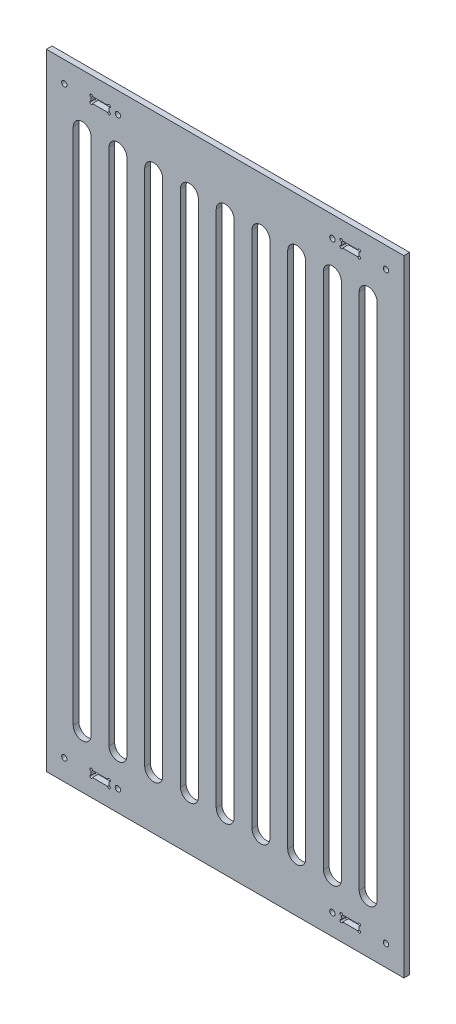
SolidWorks part; units mm, degrees
ref_plane "Front Plane" through (0, 0, 0) normal (0, 0, 1) x (1, 0, 0)
ref_plane "Top Plane" through (0, 0, 0) normal (0, 1, 0) x (1, 0, 0)
ref_plane "Right Plane" through (0, 0, 0) normal (1, 0, 0) x (0, 0, -1)
sketch "Sketch1" plane through (0, 0, 0) normal (0, 0, 1) x (1, 0, 0)
  line L5 (200, -350) -> (-200, -350)
  line L6 (200, -350) -> (200, 350)
  line L7 (200, 350) -> (-200, 350)
  line L8 (-200, -350) -> (-200, 350)
  line L9 (200, -350) -> (-200, 350) construction
  line L10 (200, 350) -> (-200, -350) construction
  point P0 (0, 0)
  dimension "D1" = 400
  dimension "D2" = 700
extrude "Boss-Extrude1" add sketch "Sketch1" along normal blind 6.35
sketch "Sketch2" plane through (0, 0, 6.35) normal (0, 0, 1) x (1, 0, 0)
  line L0 (-200, 350) -> (-200, -350) construction
  line L1 (-150, 330) -> (-130, 330)
  line L2 (-150, 330) -> (-150, 323.142)
  line L3 (-150, 323.142) -> (-130, 323.142)
  line L4 (-130, 330) -> (-130, 323.142)
  line L5 (200, 350) -> (-200, 350) construction
  circle A0 centre (-150, 330) radius 1.5
  circle A1 centre (-130, 330) radius 1.5
  circle A2 centre (-150, 323.142) radius 1.5
  circle A3 centre (-130, 323.142) radius 1.5
  circle A4 centre (-180, 326.57) radius 3
  circle A5 centre (-120, 326.57) radius 3
  dimension "D5" = 20
  dimension "D7" = 80
  dimension "D1" = 6.858
  dimension "D2" = 20
  dimension "D3" = 50
  dimension "D4" = 20
  dimension "D6" = 23.43
extrude "Cut-Extrude1" cut sketch "Sketch2" against normal through all contours A3 L4 A1 L1 A0 L2 A2 L3 | L2 A0 L1 | L1 A0 L2 | L2 A2 L3 | L3 A2 L2 | L1 A1 L4 | L4 A1 L1 | L4 A3 L3 | L3 A3 L4 | A4 | A5
mirror "Mirror1" about plane through (0, 0, 0) normal (0, 1, 0) of "Cut-Extrude1"
mirror "Mirror2" about plane through (0, 0, 0) normal (1, 0, 0) of "Mirror1", "Cut-Extrude1"
sketch "Sketch3" plane through (0, 0, 6.35) normal (0, 0, 1) x (1, 0, 0)
  line L0 (0, 290) -> (0, -290) construction
  line L1 (10, 290) -> (10, -290)
  line L2 (-10, 290) -> (-10, -290)
  line L4 (200, 350) -> (-200, 350) construction
  line L5 (-200, -350) -> (200, -350) construction
  arc A0 (10, 290) -> (-10, 290) centre (0, 290) ccw
  arc A1 (-10, -290) -> (10, -290) centre (0, -290) ccw
  point P3 (0, 0)
  dimension "D1" = 60
  dimension "D2" = 60
extrude "Cut-Extrude2" cut sketch "Sketch3" against normal through all
pattern_linear "LPattern1" count 5 spacing 40 along (1, 0, 0) of "Cut-Extrude2"
mirror "Mirror3" about plane through (0, 0, 0) normal (1, 0, 0) of "LPattern1"
